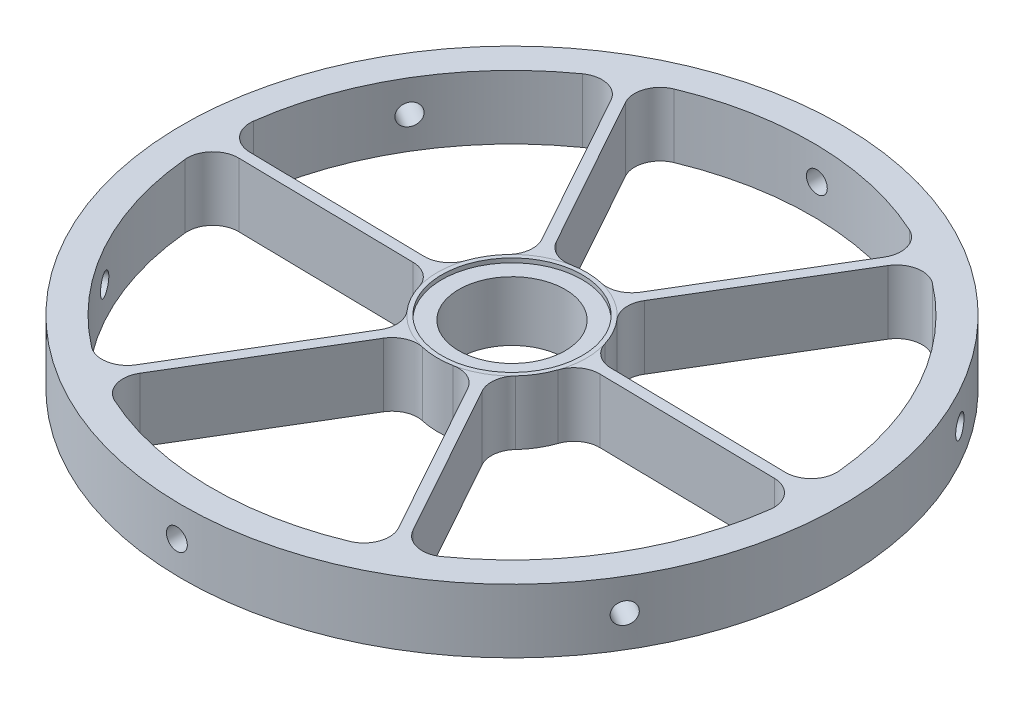
SolidWorks part; units mm, degrees
material "6061-T6 (SS)"
ref_plane "Front Plane" through (0, 0, 0) normal (0, 0, 1) x (1, 0, 0)
ref_plane "Top Plane" through (0, 0, 0) normal (0, 1, 0) x (1, 0, 0)
ref_plane "Right Plane" through (0, 0, 0) normal (1, 0, 0) x (0, 0, -1)
sketch "Center Ring" plane through (0, 0, 0) normal (0, 1, 0) x (1, 0, 0)
  circle A0 centre (0, 0) radius 15.875
  circle A1 centre (0, 0) radius 22.225
  dimension "D2" = 31.75
  dimension "D1" = 6.35
extrude "Center" add sketch "Center Ring" along normal mid plane 19.05
sketch "Outer " plane through (0, 0, 0) normal (0, 1, 0) x (1, 0, 0)
  circle A0 centre (0, 0) radius 98.425
  circle A1 centre (0, 0) radius 89.535
  dimension "D2" = 196.85
  dimension "D1" = 8.89
extrude "Outer Ring" add sketch "Outer " along normal mid plane 19.05 separate body
ref_plane "Plane1" through (0, 0, 47.625) normal (0, 0, 1) x (1, 0, 0)
sketch "beeam" plane through (0, 0, 47.625) normal (0, 0, 1) x (1, 0, 0)
  line L1 (-1.5875, -9.525) -> (1.5875, -9.525)
  line L2 (-1.5875, -9.525) -> (-1.5875, 9.525)
  line L3 (-1.5875, 9.525) -> (1.5875, 9.525)
  line L4 (1.5875, -9.525) -> (1.5875, 9.525)
  line L5 (-1.5875, -9.525) -> (1.5875, 9.525) construction
  line L6 (-1.5875, 9.525) -> (1.5875, -9.525) construction
  point P0 (0, 0)
  dimension "D1" = 3.175
  dimension "D2" = 19.05
extrude "Beam" add sketch "beeam" against normal up to surface and the other way up to surface
pattern_circular "CirPattern1" count 6 over 360 about axis through (0, 0, 0) along (0, 1, 0) of "Beam"
ref_plane "Plane2" through (0, 0, 100.0125) normal (0, 0, 1) x (1, 0, 0)
fillet "Fillet1" radius 7.62 24 edges at (78.3211, 0, 43.3856) (76.7336, 0, 46.1353) (-18.4045, 0, -12.4589) (-1.5875, 0, -22.1682) (1.5875, 0, -22.1682) (18.4045, 0, -12.4589) (19.992, 0, -9.7093) (19.992, 0, 9.7093) (18.4045, 0, 12.4589) (1.5875, 0, 22.1682) (-18.4045, 0, 12.4589) (-1.5875, 0, 22.1682) (-19.992, 0, 9.7093) (-19.992, 0, -9.7093) (1.5875, 0, 89.5209) (-1.5875, 0, 89.5209) (-76.7336, 0, 46.1353) (-78.3211, 0, 43.3856) (78.3211, 0, -43.3856) (76.7336, 0, -46.1353) (1.5875, 0, -89.5209) (-1.5875, 0, -89.5209) (-76.7336, 0, -46.1353) (-78.3211, 0, -43.3856)
sketch "Sketch9" plane through (0, 9.525, 0) normal (0, 1, 0) x (1, 0, 0)
  circle A0 centre (0, 0) radius 15.875
  dimension "D1" = 31.75
sketch "Sketch10" plane through (0, 9.525, 0) normal (0, 1, 0) x (1, 0, 0)
  circle A0 centre (0, 0) radius 22.225
  dimension "D1" = 44.45
split line "Split Line2"
ref_plane "Plane4" through (49.2125, 0, 85.2386) normal (0.5, 0, 0.866) x (0, -1, 0)
sketch "Sketch20" plane through (0, 0, 0) normal (0, 1, 0) x (1, 0, 0)
  line L1 (52.1812, -72.7574) -> (35.6077, -82.1499)
  arc A1 (10.064, -88.9676) -> (72.0162, -53.1995) centre (0, 0) ccw construction
  arc A2 (52.1812, -72.7574) -> (35.6077, -82.1499) centre (0, 0) cw
  point P3 (52.1812, -72.7574)
  point P9 (36.9386, -81.5601)
  dimension "D1" = 19.05
ref_plane "Plane6" through (0, 9.525, 0) normal (0, 1, 0) x (1, 0, 0)
sketch "Sketch27" plane through (0, 9.525, 0) normal (0, 1, 0) x (1, 0, 0)
  circle A1 centre (0, 0) radius 20.955
  arc A4 (-6.8566, 21.1409) -> (-14.8802, 16.5085) centre (0, 0) ccw construction
  dimension "05" = 1.27
extrude "Cut-Extrude3" cut sketch "Sketch27" against normal blind 1.27
ref_plane "Plane7" through (0, 0, 0) normal (0, 1, 0) x (1, 0, 0)
sketch "Sketch31" plane through (49.2125, 0, 85.2386) normal (0.5, 0, 0.866) x (0, -1, 0)
  circle A0 centre (0, 0) radius 3.175
  point P3 (3.175, 0)
  dimension "D1" = 6.35
extrude "Cut-Extrude5" cut sketch "Sketch31" against normal up to next
pattern_circular "CirPattern5" count 6 over 360 about axis through (0, 9.525, 0) along (0, -1, 0) of "Cut-Extrude5"
move or copy body "Body-Move/Copy7" bodies to move or copy 127 copy no rotation origin (0, 0, 0) rotation axis (0, -1, 0) rotation angle 31
equation "\"a\"= .125'Width of the Beams"
equation "\"D1@beeam\" = \"a\""
equation "\"T\"= .35'Width of the Outer Ring"
equation "\"D1@Outer \" = \"T\""
equation "\"R\"= .25'Thickness of the Center"
equation "\"D1@Center Ring\" = \"R\""
equation "\"H\"= .75'Height (Outer Ring/Center)"
equation "\"D1@Outer Ring\"= \"H\""
equation "\"D1@Center\"=\"H\""
equation "\"I\"= .75'Height (Beams)"
equation "\"N\"= 6'Number of Beams"
equation "\"D1@CirPattern1\"=\"N\""
equation "\"D2@beeam\"=\"I\""
equation "\"D\"= 1.5'Diameter of the Center"
